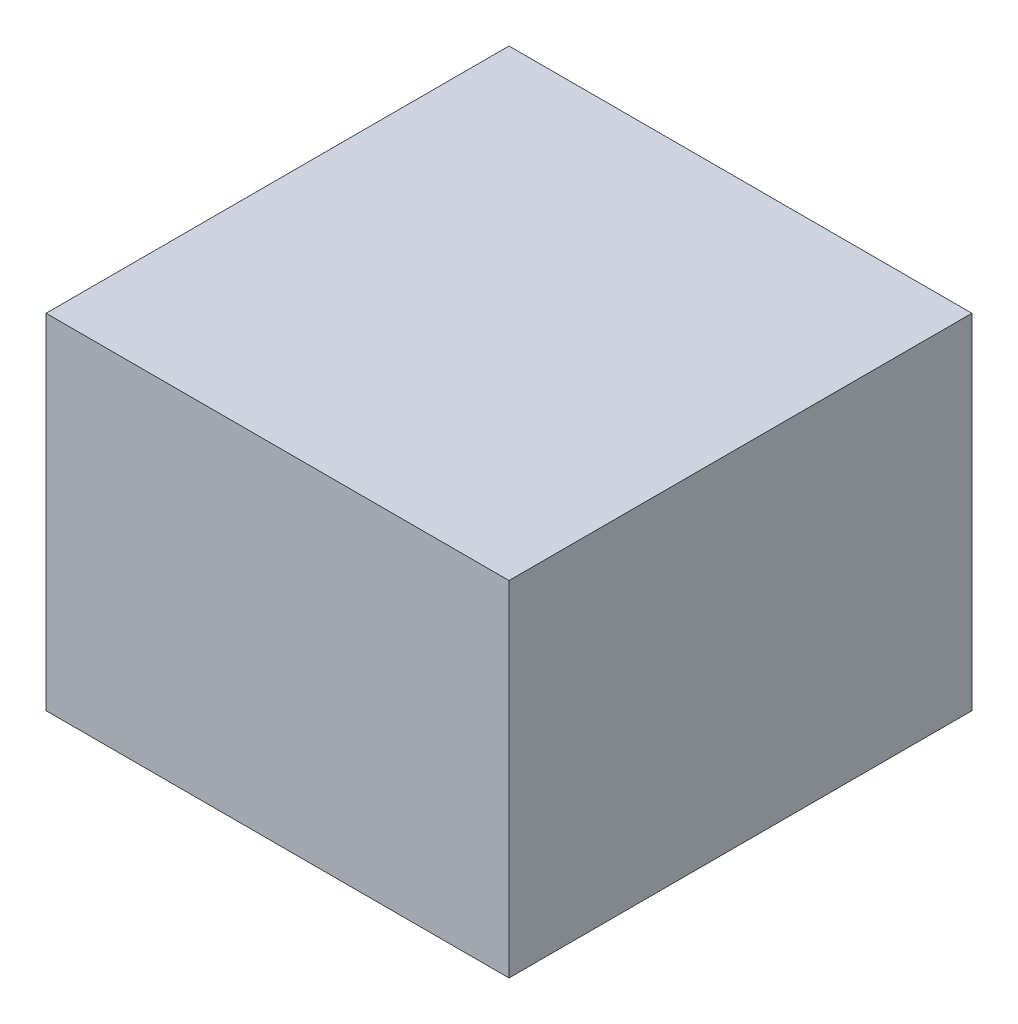
SolidWorks part; units mm, degrees
ref_plane "Front Plane" through (0, 0, 0) normal (0, 0, 1) x (1, 0, 0)
ref_plane "Top Plane" through (0, 0, 0) normal (0, 1, 0) x (1, 0, 0)
ref_plane "Right Plane" through (0, 0, 0) normal (1, 0, 0) x (0, 0, -1)
sketch "Sketch1" plane through (0, 0, 0) normal (0, 1, 0) x (1, 0, 0)
  line L1 (0, 0) -> (15.6, 0)
  line L2 (0, 0) -> (0, 15.6)
  line L3 (0, 15.6) -> (15.6, 15.6)
  line L4 (15.6, 0) -> (15.6, 15.6)
  dimension "D1" = 15.6
extrude "Boss-Extrude1" add sketch "Sketch1" along normal blind 11.6
